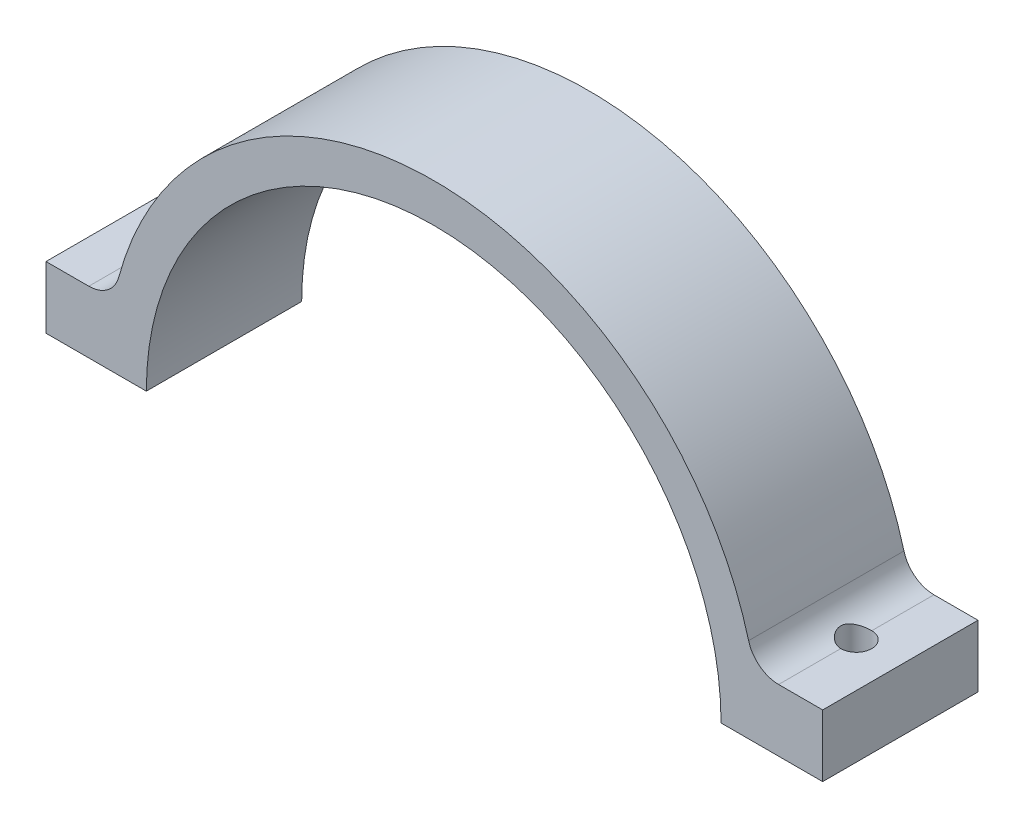
SolidWorks part; units mm, degrees
material "ABS"
ref_plane "Front Plane" through (0, 0, 0) normal (0, 0, 1) x (1, 0, 0)
ref_plane "Top Plane" through (0, 0, 0) normal (0, 1, 0) x (1, 0, 0)
ref_plane "Right Plane" through (0, 0, 0) normal (1, 0, 0) x (0, 0, -1)
sketch "Sketch1" plane through (0, 0, 0) normal (0, 0, 1) x (1, 0, 0)
  line L0 (-53.34, 0) -> (-46.99, 0)
  line L1 (46.99, 0) -> (53.34, 0)
  line L2 (-53.34, 0) -> (53.34, 0) construction
  arc A0 (53.34, 0) -> (-53.34, 0) centre (0, 0) ccw
  arc A1 (46.99, 0) -> (-46.99, 0) centre (0, 0) ccw
  dimension "D1" = 106.68
  dimension "D2" = 93.98
extrude "Boss-Extrude1" add sketch "Sketch1" along normal blind 25.4
sketch "Sketch3" plane through (0, 0, 0) normal (0, 0, -1) x (-1, 0, 0)
  line L0 (-0.1024, -54.9851) -> (-0.1024, 56.632) construction
  line L1 (63.3976, 0) -> (46.99, 0)
  line L2 (63.3976, 0) -> (63.3976, 10.16)
  line L3 (63.3976, 10.16) -> (46.99, 10.16)
  line L4 (46.99, 0) -> (46.99, 10.16)
  line L5 (114.1976, -54.9851) -> (-114.4024, -54.9851) construction
  line L6 (-47.1947, 0) -> (-47.1947, 10.16)
  line L7 (-63.6024, 10.16) -> (-47.1947, 10.16)
  line L8 (-63.6024, 0) -> (-63.6024, 10.16)
  line L9 (-63.6024, 0) -> (-47.1947, 0)
  dimension "D1" = 10.16
extrude "Boss-Extrude2" add sketch "Sketch3" against normal blind 25.4
fillet "Fillet1" radius 5.08 2 edges at (-52.3634, 10.16, 12.7) (52.3634, 10.16, 12.7)
sketch "Sketch4" plane through (0, 10.16, 0) normal (0, 1, 0) x (1, 0, 0)
  line L0 (-56.3972, -25.4) -> (-56.3972, 0) construction
  line L1 (0, 0) -> (0, -25.4) construction
  line L2 (-51.4931, -25.4) -> (51.4931, -25.4) construction
  circle A0 centre (-56.3972, -12.7) radius 2.54
  circle A1 centre (56.3972, -12.7) radius 2.54
  dimension "D1" = 5.08
extrude "Cut-Extrude1" cut sketch "Sketch4" against normal through all both and the other way through all
